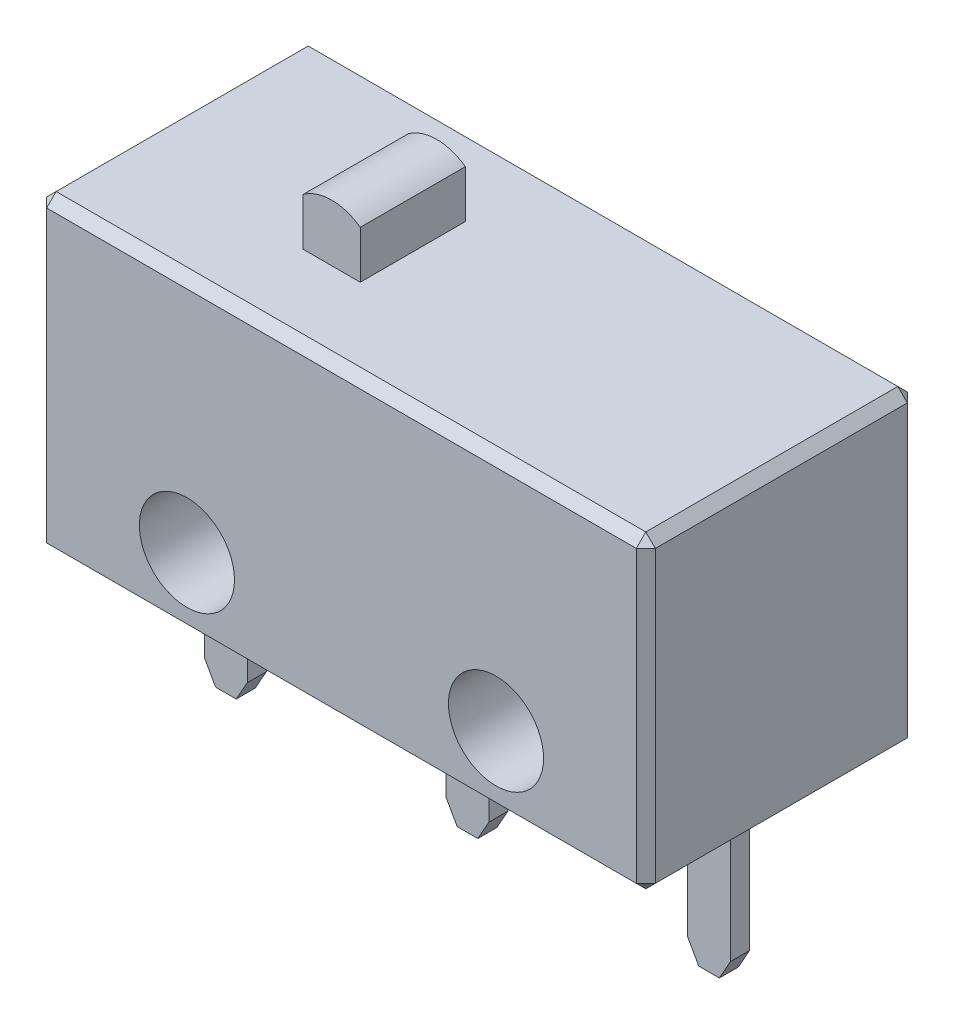
SolidWorks part; units mm, degrees
ref_plane "Front" through (0, 0, 0) normal (0, 0, 1) x (1, 0, 0)
ref_plane "Top" through (0, 0, 0) normal (0, 1, 0) x (1, 0, 0)
ref_plane "Right" through (0, 0, 0) normal (1, 0, 0) x (0, 0, -1)
sketch "Sketch2" plane through (0, 0, 0) normal (0, 0, 1) x (1, 0, 0)
  line L1 (0, 0) -> (0, 12.0432) construction
  line L2 (-6.4, 6.5) -> (-6.4, 0)
  line L3 (-6.4, 0) -> (6.4, 0)
  line L4 (6.4, 6.5) -> (6.4, 0)
  line L7 (3.25, 1.5) -> (-3.488, 1.5) construction
  line L13 (-3.25, 6.5) -> (-3.25, 1.5) construction
  line L14 (-3.012, 6.5) -> (-3.012, 3.3622) construction
  line L15 (6.4, 6.5) -> (-6.4, 6.5)
  circle A0 centre (3.25, 1.5) radius 1
  circle A1 centre (-3.25, 1.5) radius 1
  dimension "D4" = 3.25
  dimension "D5" = 2
  dimension "D7" = 6.5
  dimension "D3" = 2
  dimension "D1" = 12.8
  dimension "D2" = 1.5
extrude "Extrude1" add sketch "Sketch2" along normal mid plane 5.7
sketch "Sketch3" plane through (0, 0, 0) normal (0, 0, 1) x (1, 0, 0)
  line L0 (-2.55, 6.5) -> (-2.55, 7.5)
  line L1 (-1.95, 6.5) -> (-1.95, 6.6801) construction
  line L2 (-1.35, 7.5) -> (-1.35, 6.5)
  line L3 (-1.35, 6.5) -> (-2.55, 6.5)
  line L4 (-2.55, 7.5) -> (-1.35, 7.5) construction
  line L7 (6.4, 6.5) -> (-6.4, 6.5) construction
  arc A0 (-2.55, 7.5) -> (-1.35, 7.5) centre (-1.95, 6.6801) cw
  circle A3 centre (3.25, 1.5) radius 1 construction
  circle A4 centre (3.25, 1.5) radius 1 construction
  dimension "D1" = 5.2
  dimension "D3" = 1.016
  dimension "D2" = 1.2
  dimension "D4" = 1
extrude "Extrude2" add sketch "Sketch3" along normal mid plane 2.2098 separate body
ref_plane "Plane1" through (-7.493, 0, 0) normal (1, 0, 0) x (0, 0, -1)
sketch "Sketch12" plane through (0, 0, 0) normal (0, 0, 1) x (1, 0, 0)
  line L0 (-0.45, 0) -> (-0.45, -2.8849)
  line L1 (-6.4, 0) -> (6.4, 0) construction
  line L2 (-0.2171, -3.3) -> (0.2171, -3.3)
  line L3 (0.45, -2.8849) -> (0.45, 0)
  line L4 (0.45, 0) -> (-0.45, 0)
  line L5 (-0.45, -2.8849) -> (-0.2171, -3.3)
  line L6 (0.45, -2.8849) -> (0.2171, -3.3)
  line L7 (0, 0) -> (0, -4.911) construction
  line L8 (-2.54, 4.6888) -> (-2.54, -5.3831) construction
  line L9 (2.54, 4.6888) -> (2.54, -5.3831) construction
  line L10 (-5.53, -2.8849) -> (-5.2971, -3.3)
  line L11 (-4.63, -2.8849) -> (-4.8629, -3.3)
  line L12 (-5.53, 0) -> (-4.63, 0)
  line L13 (-5.53, -2.8849) -> (-5.53, 0)
  line L14 (-4.8629, -3.3) -> (-5.2971, -3.3)
  line L15 (-4.63, 0) -> (-4.63, -2.8849)
  line L16 (4.63, -2.8849) -> (4.8629, -3.3)
  line L17 (5.53, -2.8849) -> (5.2971, -3.3)
  line L18 (4.63, 0) -> (5.53, 0)
  line L19 (4.63, -2.8849) -> (4.63, 0)
  line L20 (5.2971, -3.3) -> (4.8629, -3.3)
  line L21 (5.53, 0) -> (5.53, -2.8849)
  dimension "D1" = 0.9
  dimension "D2" = 3.3
  dimension "D3" = 0.4341
  dimension "D4" = 2.54
  dimension "D5" = 2.54
extrude "Boss-Extrude2" add sketch "Sketch12" along normal mid plane 0.4
chamfer "Chamfer1" distance 0.2 angle 45 12 edges at (0, 6.5, -2.85) (-6.4, 3.25, -2.85) (0, 0, -2.85) (6.4, 3.25, -2.85) (0, 0, 2.85) (-6.4, 3.25, 2.85) (0, 6.5, 2.85) (6.4, 3.25, 2.85) (6.4, 0, 0) (6.4, 6.5, 0) (-6.4, 6.5, 0) (-6.4, 0, 0)
